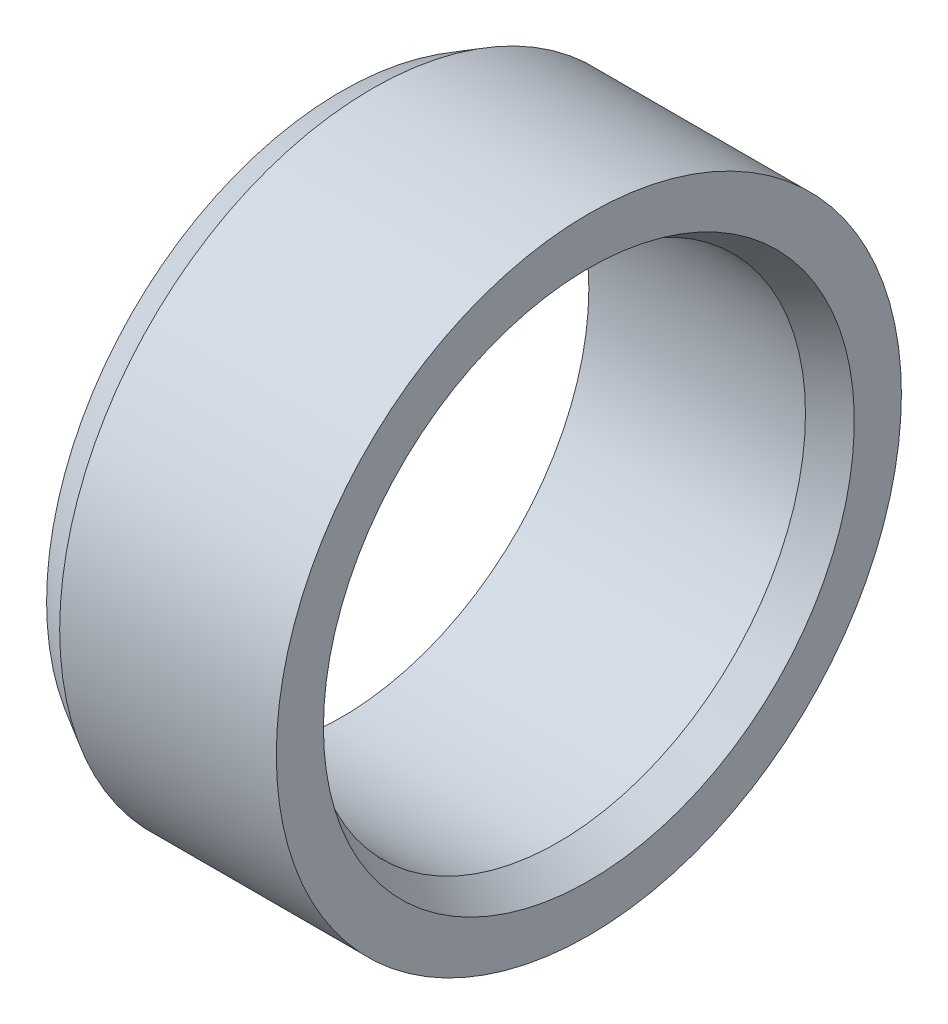
SolidWorks part; units mm, degrees
ref_plane "Vorne" through (0, 0, 0) normal (0, 0, 1) x (1, 0, 0)
ref_plane "Oben" through (0, 0, 0) normal (0, 1, 0) x (1, 0, 0)
ref_plane "Rechts" through (0, 0, 0) normal (1, 0, 0) x (0, 0, -1)
sketch "Skizze1" plane through (0, 0, 0) normal (0, 1, 0) x (1, 0, 0)
  line L0 (-1.5, 5.05) -> (2, 5.05)
  line L1 (2, 5.05) -> (2, 4.2887)
  line L2 (2, 4.2887) -> (1.5, 4)
  line L3 (1.5, 4) -> (-2, 4)
  line L4 (-2, 4) -> (-2, 4.7613)
  line L5 (-2, 4.7613) -> (-1.5, 5.05)
  line L6 (-2, 0) -> (2, 0) construction
  dimension "D1" = 30
  dimension "D2" = 30
  dimension "D3" = 0.5
  dimension "D4" = 0.5
  dimension "D5" = 4
  dimension "D6" = 2
  dimension "D7" = 4
  dimension "D8" = 5.05
revolve "Rotation1" add sketch "Skizze1" angle 360 about L6
equation "\"D6@Skizze1\"=\"D5@Skizze1\"/2"
